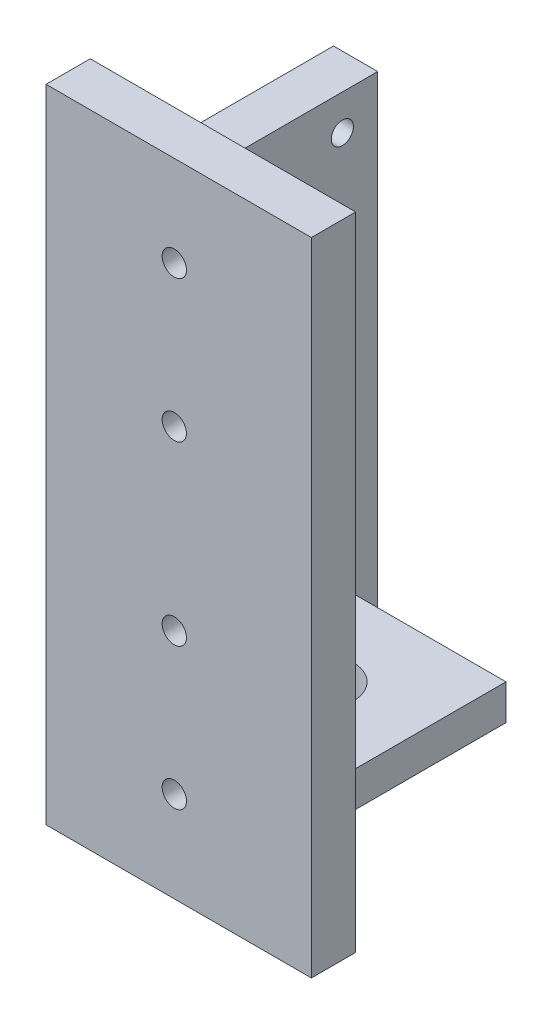
SolidWorks part; units mm, degrees
ref_plane "Plan de face" through (0, 0, 0) normal (0, 0, 1) x (1, 0, 0)
ref_plane "Plan de dessus" through (0, 0, 0) normal (0, 1, 0) x (1, 0, 0)
ref_plane "Plan de droite" through (0, 0, 0) normal (1, 0, 0) x (0, 0, -1)
sketch "Sketch1" plane through (0, 0, 0) normal (0, 0, 1) x (1, 0, 0)
  line L1 (-2, -9.798) -> (8, -9.798)
  line L2 (-2, -9.798) -> (-2, 110.202)
  line L3 (-2, 110.202) -> (8, 110.202)
  line L4 (8, -9.798) -> (8, 110.202)
  dimension "D1" = 10
  dimension "D2" = 120
  dimension "D3" = 10
  dimension "D4" = 8
extrude "Boss-Extrude1" add sketch "Sketch1" along normal blind 55
sketch "Sketch2" plane through (8, 0, 0) normal (1, 0, 0) x (0, 0, -1)
  line L0 (-55, 10.202) -> (-55, 18.202)
  line L2 (-55, -9.798) -> (-55, 110.202) construction
  line L5 (-55, 18.202) -> (-13, 18.202)
  line L6 (-13, 18.202) -> (-13, 10.202)
  line L7 (-13, 10.202) -> (-55, 10.202)
  line L8 (-55, -9.798) -> (0, -9.798) construction
  dimension "D1" = 8
  dimension "D4" = 20
  dimension "D6" = 42
extrude "Boss-Extrude2" add sketch "Sketch2" along normal blind 42 contours L5 L6 L7 L0
sketch "Sketch3" plane through (0, 10.202, 0) normal (0, -1, 0) x (1, 0, 0)
  line L0 (50, 34) -> (8, 34) construction
  line L1 (50, 55) -> (50, 13) construction
  line L2 (8, 55) -> (8, 13) construction
  circle A0 centre (29, 34) radius 7.5
  dimension "D1" = 15
extrude "Cut-Extrude1" cut sketch "Sketch3" against normal up to surface (8 mm away) contours A0 up to face at (34.25, 18.202, 39.25)
sketch "Sketch4" plane through (0, 0, 13) normal (0, 0, -1) x (-1, 0, 0)
  line L1 (-50, 10.202) -> (-58, 10.202)
  line L2 (-50, 10.202) -> (-50, 54.202)
  line L3 (-50, 54.202) -> (-58, 54.202)
  line L4 (-58, 10.202) -> (-58, 54.202)
  dimension "D1" = 36
  dimension "D2" = 8
extrude "Boss-Extrude3" [suppressed] add sketch "Sketch4" against normal up to surface (327.3012 mm away) contours L4 L3 L2 L1
sketch "Sketch5" plane through (0, 0, 55) normal (0, 0, 1) x (1, 0, 0)
  line L1 (-2, -9.798) -> (58, -9.798)
  line L2 (-2, -9.798) -> (-2, 135.202)
  line L3 (-2, 135.202) -> (58, 135.202)
  line L4 (58, -9.798) -> (58, 135.202)
  dimension "D1" = 145
  dimension "D2" = 60
extrude "Boss-Extrude4" add sketch "Sketch5" along normal blind 10
sketch "Sketch6" plane through (0, 0, 65) normal (0, 0, 1) x (1, 0, 0)
  line L2 (58, -9.798) -> (58, 135.202) construction
  line L3 (58, 135.202) -> (-2, 135.202) construction
  circle A0 centre (27, 114.702) radius 2.75
  circle A1 centre (27, 82.702) radius 2.75
  circle A2 centre (27, 42.702) radius 2.75
  circle A3 centre (27, 10.702) radius 2.75
  dimension "D1" = 5.5
  dimension "D2" = 5.5
  dimension "D3" = 5.5
  dimension "D4" = 5.5
  dimension "D5" = 40
  dimension "D6" = 32
  dimension "D7" = 32
  dimension "D8" = 20.5
  dimension "D9" = 31
extrude "Cut-Extrude2" cut sketch "Sketch6" against normal up to surface (10 mm away) up to face at (26.6, 48.452, 55)
sketch "Sketch7" plane through (8, 0, 0) normal (1, 0, 0) x (0, 0, -1)
  line L0 (0, 50.202) -> (-10.1246, 50.202) construction
  line L1 (0, -9.798) -> (0, 110.202) construction
  line L2 (-55, 110.202) -> (0, 110.202) construction
  line L3 (-55, 18.202) -> (-55, 110.202) construction
  circle A0 centre (-47, 102.202) radius 2.5
  circle A1 centre (-8, 102.202) radius 2.5
  circle A2 centre (-47, -1.798) radius 2.5
  circle A3 centre (-8, -1.798) radius 2.5
  dimension "D1" = 5
  dimension "D2" = 5
  dimension "D3" = 8
  dimension "D4" = 8
  dimension "D5" = 8
extrude "Cut-Extrude3" cut sketch "Sketch7" against normal blind 10
